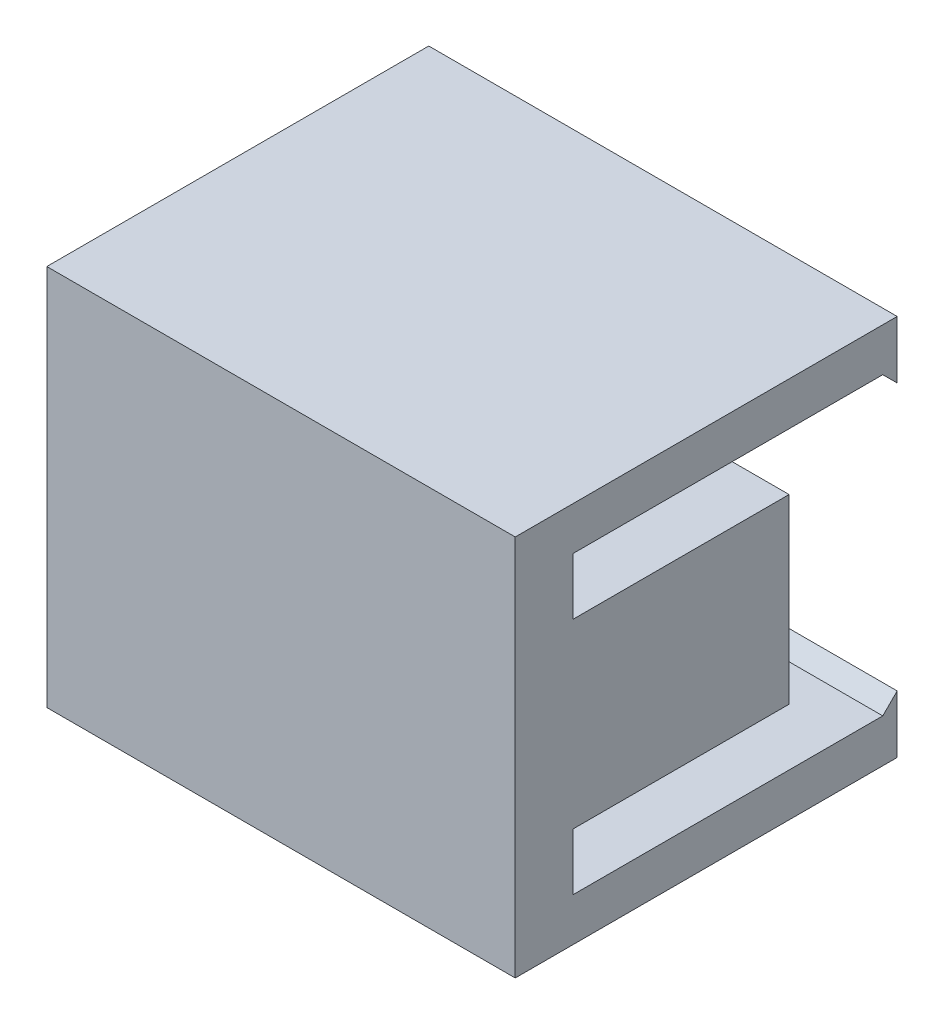
SolidWorks part; units mm, degrees
ref_plane "Front Plane" through (0, 0, 0) normal (0, 0, 1) x (1, 0, 0)
ref_plane "Top Plane" through (0, 0, 0) normal (0, 1, 0) x (1, 0, 0)
ref_plane "Right Plane" through (0, 0, 0) normal (1, 0, 0) x (0, 0, -1)
sketch "Sketch1" plane through (0, 0, 0) normal (0, 0, 1) x (1, 0, 0)
  line L1 (-16.25, 13.25) -> (16.25, 13.25)
  line L2 (-16.25, 13.25) -> (-16.25, -13.25)
  line L3 (-16.25, -13.25) -> (16.25, -13.25)
  line L4 (16.25, 13.25) -> (16.25, -13.25)
  line L5 (-16.25, 13.25) -> (16.25, -13.25) construction
  line L6 (-16.25, -13.25) -> (16.25, 13.25) construction
  point P0 (0, 0)
extrude "Boss-Extrude1" add sketch "Sketch1" along normal blind 4
sketch "Sketch2" plane through (0, 0, 0) normal (0, 0, -1) x (-1, 0, 0)
  line L0 (-16.25, 0) -> (-9.75, 0)
  line L1 (-16.25, -13.25) -> (-16.25, 13.25) construction
  line L3 (-9.75, -6.3) -> (-16.25, -6.3)
  line L4 (-9.75, -6.3) -> (-9.75, 6.3)
  line L5 (-9.75, 6.3) -> (-16.25, 6.3)
  line L6 (-16.25, -6.3) -> (-16.25, 6.3)
  line L7 (-9.75, -6.3) -> (-16.25, 6.3) construction
  line L8 (-9.75, 6.3) -> (-16.25, -6.3) construction
  point P5 (-13, 0)
  line M6 (-16.25, 13.25) -> (-16.25, -13.25)
extrude "Boss-Extrude2" add sketch "Sketch2" along normal blind 15 contours L3 L4 L0 M6 | L4 L5 L0 M6
sketch "Sketch3" plane through (0, 0, 0) normal (0, 0, -1) x (-1, 0, 0)
  line L0 (-16.25, -13.25) -> (-16.25, -10.25)
  line L1 (16.25, -13.25) -> (-16.25, -13.25) construction
  line L2 (-16.25, -13.25) -> (-16.25, -6.3) construction
  line L3 (-16.25, 13.25) -> (-16.25, 10.25)
  line L4 (-16.25, 6.3) -> (-16.25, 13.25) construction
  line L6 (-16.25, -10.25) -> (16.25, -10.25)
  line L7 (-16.25, -10.25) -> (-16.25, -13.25)
  line L8 (-16.25, -13.25) -> (16.25, -13.25)
  line L9 (16.25, -10.25) -> (16.25, -13.25)
  line L10 (-16.25, 10.25) -> (16.25, 10.25)
  line L11 (-16.25, 10.25) -> (-16.25, 13.25)
  line L12 (-16.25, 13.25) -> (16.25, 13.25)
  line L13 (16.25, 10.25) -> (16.25, 13.25)
  line M13 (-16.25, -6.3) -> (-16.25, -13.25)
  line M14 (-16.25, -13.25) -> (16.25, -13.25)
  line M15 (16.25, -13.25) -> (16.25, 13.25)
  line M16 (16.25, 13.25) -> (-16.25, 13.25)
  line M17 (-16.25, 13.25) -> (-16.25, 6.3)
extrude "Boss-Extrude3" add sketch "Sketch3" along normal blind 22.5 contours L6 M13 M14 M15 | L10 M17 M15 M16
sketch "Sketch4" plane through (0, -10.25, 0) normal (0, 1, 0) x (1, 0, 0)
  line L0 (-16.25, 22.5) -> (-16.25, 21.5)
  line L1 (-16.25, 22.5) -> (-16.25, 0) construction
  line L3 (-16.25, 21.5) -> (16.25, 21.5)
  line L4 (-16.25, 21.5) -> (-16.25, 22.5)
  line L5 (-16.25, 22.5) -> (16.25, 22.5)
  line L6 (16.25, 21.5) -> (16.25, 22.5)
  line M3 (16.25, 0) -> (16.25, 22.5)
  line M4 (16.25, 22.5) -> (-16.25, 22.5)
  line M5 (-16.25, 22.5) -> (-16.25, 0)
extrude "Boss-Extrude4" add sketch "Sketch4" along normal blind 1 contours L3 M5 M3 M4
sketch "Sketch5" plane through (-16.25, 0, 0) normal (-1, 0, 0) x (0, 0, 1)
  line L0 (-21.5, -10.25) -> (-22.5, -9.25)
  line L1 (-22.5, -9.25) -> (-21.5, -9.25)
  line L2 (-21.5, -9.25) -> (-21.5, -10.25)
extrude "Cut-Extrude1" cut sketch "Sketch5" against normal through all
sketch "Sketch6" plane through (0, 10.25, 0) normal (0, -1, 0) x (1, 0, 0)
  line L0 (-16.25, -22.5) -> (-16.25, -21.5)
  line L1 (-16.25, -22.5) -> (-16.25, 0) construction
  line L3 (-16.25, -21.5) -> (16.25, -21.5)
  line L4 (-16.25, -21.5) -> (-16.25, -22.5)
  line L5 (-16.25, -22.5) -> (16.25, -22.5)
  line L6 (16.25, -21.5) -> (16.25, -22.5)
extrude "Boss-Extrude5" add sketch "Sketch6" along normal blind 1 contours L4 L3 L6 L5
sketch "Sketch7" plane through (-16.25, 0, 0) normal (-1, 0, 0) x (0, 0, 1)
  line L0 (-21.5, 10.25) -> (-21.5, 9.25)
  line L1 (-21.5, 9.25) -> (-22.5, 9.25)
  line L2 (-22.5, 9.25) -> (-21.5, 10.25)
extrude "Cut-Extrude2" cut sketch "Sketch7" against normal through all
sketch "Sketch8" plane through (0, 0, 0) normal (0, 0, -1) x (-1, 0, 0)
  line L0 (16.25, 0) -> (16.25, -2.0199)
  line L1 (16.25, 10.25) -> (16.25, -10.25) construction
  line L2 (16.25, 0) -> (16.25, 2)
  line L3 (16.25, -2.0199) -> (16.25, -5.5199)
  line L4 (16.25, 2) -> (16.25, 5.5)
  line L5 (16.25, -2.0199) -> (13.25, -2.0199)
  line L6 (16.25, -2.0199) -> (16.25, -5.5199)
  line L7 (16.25, -5.5199) -> (13.25, -5.5199)
  line L8 (13.25, -2.0199) -> (13.25, -5.5199)
  line L10 (16.25, 5.5) -> (13.25, 5.5)
  line L11 (16.25, 5.5) -> (16.25, 2)
  line L12 (16.25, 2) -> (13.25, 2)
  line L13 (13.25, 5.5) -> (13.25, 2)
  line M20 (16.25, -10.25) -> (16.25, 10.25)
extrude "Boss-Extrude6" add sketch "Sketch8" along normal blind 15 contours L10 L13 L12 M20 | L5 L8 L7 M20
